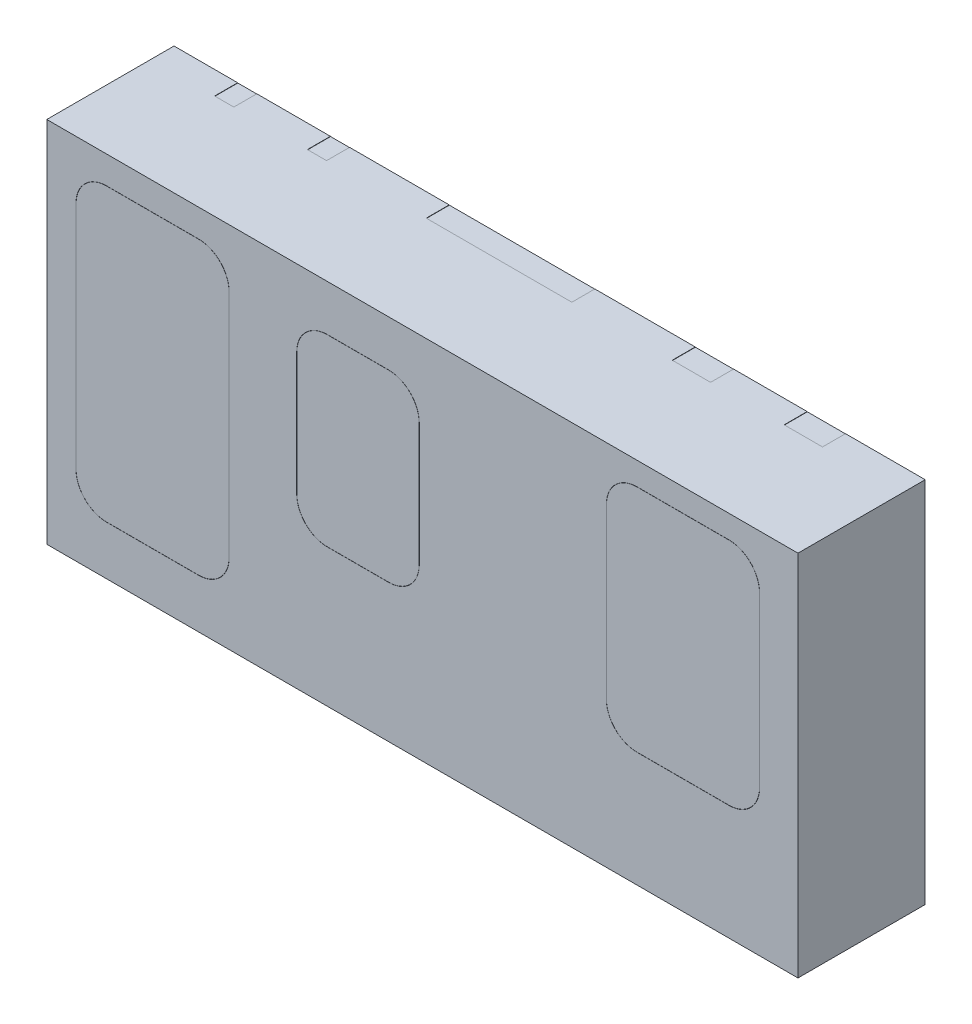
SolidWorks part; units mm, degrees
ref_plane "Спереди" through (0, 0, 0) normal (0, 0, 1) x (1, 0, 0)
ref_plane "Сверху" through (0, 0, 0) normal (0, 1, 0) x (1, 0, 0)
ref_plane "Справа" through (0, 0, 0) normal (1, 0, 0) x (0, 0, -1)
sketch "Эскиз1" plane through (0, 0, 0) normal (0, 0, 1) x (1, 0, 0)
  line L1 (0, 0) -> (4.9, 0)
  line L2 (0, 0) -> (0, 2.4)
  line L3 (0, 2.4) -> (4.9, 2.4)
  line L4 (4.9, 0) -> (4.9, 2.4)
  dimension "D1" = 4.9
  dimension "D2" = 2.4
extrude "Основание-Вытянуть" add sketch "Эскиз1" along normal blind 0.83
sketch "Эскиз2" plane through (0, 0, 0.83) normal (0, 0, 1) x (1, 0, 0)
  line L0 (0.69, 2.22) -> (0.69, 0.32) construction
  line L1 (3.85, 2.25) -> (4.45, 2.25)
  line L2 (3.65, 2.05) -> (3.65, 0.95)
  line L3 (3.85, 0.75) -> (4.45, 0.75)
  line L4 (4.65, 2.05) -> (4.65, 0.95)
  line L5 (1.83, 2.1) -> (2.23, 2.1)
  line L6 (1.63, 1.9) -> (1.63, 1.1)
  line L7 (1.83, 0.9) -> (2.23, 0.9)
  line L8 (2.43, 1.9) -> (2.43, 1.1)
  line L9 (0.39, 2.22) -> (0.99, 2.22)
  line L10 (0.19, 2.02) -> (0.19, 0.52)
  line L11 (0.39, 0.32) -> (0.99, 0.32)
  line L12 (1.19, 2.02) -> (1.19, 0.52)
  line L13 (2.03, 2.1) -> (2.03, 0.9) construction
  line L14 (4.15, 2.25) -> (4.15, 0.75) construction
  line L15 (0, 2.4) -> (0, 0) construction
  line L16 (0.19, 1.27) -> (1.19, 1.27) construction
  line L17 (1.63, 1.5) -> (2.43, 1.5) construction
  line L18 (3.65, 1.5) -> (4.65, 1.5) construction
  line L19 (0, 0) -> (4.9, 0) construction
  arc A0 (0.19, 0.52) -> (0.39, 0.32) centre (0.39, 0.52) ccw
  arc A1 (0.99, 0.32) -> (1.19, 0.52) centre (0.99, 0.52) ccw
  arc A2 (0.99, 2.22) -> (1.19, 2.02) centre (0.99, 2.02) cw
  arc A3 (0.39, 2.22) -> (0.19, 2.02) centre (0.39, 2.02) ccw
  arc A4 (1.83, 2.1) -> (1.63, 1.9) centre (1.83, 1.9) ccw
  arc A5 (2.23, 2.1) -> (2.43, 1.9) centre (2.23, 1.9) cw
  arc A6 (2.23, 0.9) -> (2.43, 1.1) centre (2.23, 1.1) ccw
  arc A7 (1.63, 1.1) -> (1.83, 0.9) centre (1.83, 1.1) ccw
  arc A8 (3.65, 0.95) -> (3.85, 0.75) centre (3.85, 0.95) ccw
  arc A9 (4.45, 0.75) -> (4.65, 0.95) centre (4.45, 0.95) ccw
  arc A10 (4.45, 2.25) -> (4.65, 2.05) centre (4.45, 2.05) cw
  arc A11 (3.85, 2.25) -> (3.65, 2.05) centre (3.85, 2.05) ccw
  dimension "D11" = 0.2
  dimension "D1" = 1
  dimension "D2" = 0.69
  dimension "D3" = 2.03
  dimension "D4" = 4.15
  dimension "D5" = 0.8
  dimension "D6" = 1.5
  dimension "D7" = 1.27
  dimension "D8" = 1.9
  dimension "D9" = 1.2
  dimension "D10" = 1.5
extrude "Вырез-Вытянуть1" cut sketch "Эскиз2" against normal blind 0.1
sketch "Эскиз3" plane through (0, 0, 0) normal (0, 0, -1) x (-1, 0, 0)
  line L0 (-4.9, 2.4) -> (0, 2.4) construction
  line L1 (-0.225, 1.2) -> (-1.335, 1.2)
  line L2 (-0.225, 1.2) -> (-0.225, 2.24)
  line L3 (-0.225, 2.24) -> (-0.415, 2.24)
  line L4 (-1.335, 1.2) -> (-1.335, 2.24)
  line L5 (-1.62, 0.9) -> (-2.92, 0.9)
  line L6 (-1.62, 0.9) -> (-1.62, 2.24)
  line L7 (-1.62, 2.24) -> (-1.795, 2.24)
  line L8 (-2.92, 0.9) -> (-2.92, 2.24)
  line L9 (-3.24, 0.9) -> (-4.54, 0.9)
  line L10 (-3.24, 0.9) -> (-3.24, 2.24)
  line L11 (-3.24, 2.24) -> (-3.4, 2.24)
  line L12 (-4.54, 0.9) -> (-4.54, 2.24)
  line L13 (-0.65, 0) -> (-0.65, 0.8037) construction
  line L14 (-1.795, 2.24) -> (-1.795, 2.4)
  line L15 (-1.795, 2.4) -> (-2.745, 2.4)
  line L16 (-2.745, 2.24) -> (-2.745, 2.4)
  line L17 (0, 0) -> (-4.9, 0) construction
  line L18 (-1.335, 0) -> (-1.335, 0.6958) construction
  line L19 (-0.415, 2.24) -> (-0.415, 2.4)
  line L20 (-0.415, 2.4) -> (-0.54, 2.4)
  line L21 (-1.145, 2.24) -> (-1.145, 2.4)
  line L22 (-2.02, 0) -> (-2.02, 0.6958) construction
  line L23 (-3.4, 2.24) -> (-3.4, 2.4)
  line L24 (-3.4, 2.4) -> (-3.65, 2.4)
  line L25 (-4.38, 2.24) -> (-4.38, 2.4)
  line L26 (-0.5, 0) -> (-0.8, 0)
  line L27 (-0.5, 0) -> (-0.5, 0.55)
  line L28 (-0.8, 0.55) -> (-0.9, 0.55)
  line L29 (-0.8, 0) -> (-0.8, 0.55)
  line L30 (-4.38, 2.24) -> (-4.54, 2.24)
  line L31 (-1.485, 0) -> (-1.185, 0)
  line L32 (-1.485, 0) -> (-1.485, 0.55)
  line L33 (-1.485, 0.55) -> (-1.385, 0.55)
  line L34 (-1.185, 0) -> (-1.185, 1)
  line L35 (-2.17, 0) -> (-1.87, 0)
  line L36 (-2.17, 0) -> (-2.17, 0.55)
  line L37 (-2.17, 0.55) -> (-1.87, 0.55)
  line L38 (-1.87, 0) -> (-1.87, 0.55)
  line L39 (-2.855, 0) -> (-2.555, 0)
  line L40 (-2.855, 0) -> (-2.855, 0.55)
  line L41 (-2.855, 0.55) -> (-2.555, 0.55)
  line L42 (-2.555, 0) -> (-2.555, 0.55)
  line L43 (-3.54, 0) -> (-3.24, 0)
  line L44 (-3.54, 0) -> (-3.54, 0.55)
  line L45 (-3.54, 0.55) -> (-3.24, 0.55)
  line L46 (-3.24, 0) -> (-3.24, 0.55)
  line L47 (-2.745, 2.24) -> (-2.92, 2.24)
  line L48 (-1.145, 2.24) -> (-1.335, 2.24)
  line L49 (-2.705, 0) -> (-2.705, 0.5973) construction
  line L50 (-3.39, 0) -> (-3.39, 0.5973) construction
  line L51 (0, 2.4) -> (0, 0) construction
  line L52 (-1.385, 0.55) -> (-1.385, 1)
  line L53 (-4.13, 2.4) -> (-4.38, 2.4)
  line L54 (-0.25, 0.55) -> (-0.5, 0.55)
  line L55 (-1.385, 1) -> (-1.185, 1)
  line L56 (-0.25, 0.55) -> (-0.25, 1)
  line L57 (-0.25, 1) -> (-0.9, 1)
  line L58 (-0.9, 0.55) -> (-0.9, 1)
  line L59 (-1.02, 2.4) -> (-1.145, 2.4)
  line L60 (-0.78, 2.4) -> (-0.78, 1.2) construction
  line L61 (-3.89, 2.4) -> (-3.89, 0.9) construction
  line L62 (-2.27, 2.4) -> (-2.27, 0.9) construction
  arc A0 (-4.13, 2.4) -> (-3.65, 2.4) centre (-3.89, 2.4) ccw
  arc A1 (-1.02, 2.4) -> (-0.54, 2.4) centre (-0.78, 2.4) ccw
  dimension "D14" = 0.48
  dimension "D1" = 0.65
  dimension "D2" = 0.685
  dimension "D3" = 0.685
  dimension "D4" = 0.685
  dimension "D5" = 0.685
  dimension "D6" = 0.3
  dimension "D7" = 0.55
  dimension "D8" = 0.2
  dimension "D9" = 1
  dimension "D10" = 0.65
  dimension "D11" = 0.73
  dimension "D12" = 0.95
  dimension "D13" = 0.98
  dimension "D15" = 1.5
  dimension "D16" = 0.78
  dimension "D17" = 1.49
  dimension "D18" = 1.62
  dimension "D19" = 1.2
  dimension "D20" = 1.3
  dimension "D21" = 0.16
extrude "Вырез-Вытянуть2" cut sketch "Эскиз3" against normal blind 0.15
sketch "Эскиз4" plane through (0, 0, 0.15) normal (0, 0, -1) x (-1, 0, 0)
  line L16 (-0.501, 0.001) -> (-0.501, 0.551)
  line L17 (-0.501, 0.551) -> (-0.251, 0.551)
  line L18 (-0.251, 0.551) -> (-0.251, 0.999)
  line L19 (-0.251, 0.999) -> (-0.899, 0.999)
  line L20 (-0.899, 0.999) -> (-0.899, 0.551)
  line L21 (-0.899, 0.551) -> (-0.799, 0.551)
  line L22 (-0.799, 0.551) -> (-0.799, 0.001)
  line L23 (-0.799, 0.001) -> (-0.501, 0.001)
  line L24 (-0.501, 0.001) -> (-0.501, 0.551)
  line L25 (-0.501, 0.551) -> (-0.251, 0.551)
  line L26 (-0.251, 0.551) -> (-0.251, 0.999)
  line L27 (-0.251, 0.999) -> (-0.899, 0.999)
  line L28 (-0.899, 0.999) -> (-0.899, 0.551)
  line L29 (-0.899, 0.551) -> (-0.799, 0.551)
  line L30 (-0.799, 0.551) -> (-0.799, 0.001)
  line L31 (-0.799, 0.001) -> (-0.501, 0.001)
  dimension "D1" = 0.001
extrude "Бобышка-Вытянуть1" add sketch "Эскиз4" along normal up to surface (0.15 mm away)
sketch "Эскиз5" plane through (0, 0, 0.15) normal (0, 0, -1) x (-1, 0, 0)
  line L18 (-1.484, 0.549) -> (-1.484, 0.001)
  line L19 (-1.484, 0.001) -> (-1.186, 0.001)
  line L20 (-1.186, 0.001) -> (-1.186, 0.999)
  line L21 (-1.186, 0.999) -> (-1.384, 0.999)
  line L22 (-1.384, 0.999) -> (-1.384, 0.549)
  line L23 (-1.384, 0.549) -> (-1.484, 0.549)
  line L24 (-1.484, 0.549) -> (-1.484, 0.001)
  line L25 (-1.484, 0.001) -> (-1.186, 0.001)
  line L26 (-1.186, 0.001) -> (-1.186, 0.999)
  line L27 (-1.186, 0.999) -> (-1.384, 0.999)
  line L28 (-1.384, 0.999) -> (-1.384, 0.549)
  line L29 (-1.384, 0.549) -> (-1.484, 0.549)
  line L32 (-2.169, 0.549) -> (-2.169, 0.001)
  line L33 (-2.169, 0.001) -> (-1.871, 0.001)
  line L34 (-1.871, 0.001) -> (-1.871, 0.549)
  line L35 (-1.871, 0.549) -> (-2.169, 0.549)
  line L36 (-2.169, 0.549) -> (-2.169, 0.001)
  line L37 (-2.169, 0.001) -> (-1.871, 0.001)
  line L38 (-1.871, 0.001) -> (-1.871, 0.549)
  line L39 (-1.871, 0.549) -> (-2.169, 0.549)
  line L44 (-2.854, 0.549) -> (-2.854, 0.001)
  line L45 (-2.854, 0.001) -> (-2.556, 0.001)
  line L46 (-2.556, 0.001) -> (-2.556, 0.549)
  line L47 (-2.556, 0.549) -> (-2.854, 0.549)
  line L48 (-2.854, 0.549) -> (-2.854, 0.001)
  line L49 (-2.854, 0.001) -> (-2.556, 0.001)
  line L50 (-2.556, 0.001) -> (-2.556, 0.549)
  line L51 (-2.556, 0.549) -> (-2.854, 0.549)
  line L56 (-3.539, 0.549) -> (-3.539, 0.001)
  line L57 (-3.539, 0.001) -> (-3.241, 0.001)
  line L58 (-3.241, 0.001) -> (-3.241, 0.549)
  line L59 (-3.241, 0.549) -> (-3.539, 0.549)
  line L60 (-3.539, 0.549) -> (-3.539, 0.001)
  line L61 (-3.539, 0.001) -> (-3.241, 0.001)
  line L62 (-3.241, 0.001) -> (-3.241, 0.549)
  line L63 (-3.241, 0.549) -> (-3.539, 0.549)
  line L78 (-3.241, 0.901) -> (-3.241, 2.239)
  line L79 (-3.241, 2.239) -> (-3.401, 2.239)
  line L80 (-3.401, 2.239) -> (-3.401, 2.399)
  line L81 (-3.401, 2.399) -> (-3.649, 2.399)
  line L82 (-4.131, 2.399) -> (-4.379, 2.399)
  line L83 (-4.379, 2.399) -> (-4.379, 2.239)
  line L84 (-4.379, 2.239) -> (-4.539, 2.239)
  line L85 (-4.539, 2.239) -> (-4.539, 0.901)
  line L86 (-4.539, 0.901) -> (-3.241, 0.901)
  line L87 (-3.241, 0.901) -> (-3.241, 2.239)
  line L88 (-3.241, 2.239) -> (-3.401, 2.239)
  line L89 (-3.401, 2.239) -> (-3.401, 2.399)
  line L90 (-3.401, 2.399) -> (-3.649, 2.399)
  line L91 (-4.131, 2.399) -> (-4.379, 2.399)
  line L92 (-4.379, 2.399) -> (-4.379, 2.239)
  line L93 (-4.379, 2.239) -> (-4.539, 2.239)
  line L94 (-4.539, 2.239) -> (-4.539, 0.901)
  line L95 (-4.539, 0.901) -> (-3.241, 0.901)
  line L103 (-1.621, 0.901) -> (-1.621, 2.239)
  line L104 (-1.621, 2.239) -> (-1.796, 2.239)
  line L105 (-1.796, 2.239) -> (-1.796, 2.399)
  line L106 (-1.796, 2.399) -> (-2.744, 2.399)
  line L107 (-2.744, 2.399) -> (-2.744, 2.239)
  line L108 (-2.744, 2.239) -> (-2.919, 2.239)
  line L109 (-2.919, 2.239) -> (-2.919, 0.901)
  line L110 (-2.919, 0.901) -> (-1.621, 0.901)
  line L111 (-1.621, 0.901) -> (-1.621, 2.239)
  line L112 (-1.621, 2.239) -> (-1.796, 2.239)
  line L113 (-1.796, 2.239) -> (-1.796, 2.399)
  line L114 (-1.796, 2.399) -> (-2.744, 2.399)
  line L115 (-2.744, 2.399) -> (-2.744, 2.239)
  line L116 (-2.744, 2.239) -> (-2.919, 2.239)
  line L117 (-2.919, 2.239) -> (-2.919, 0.901)
  line L118 (-2.919, 0.901) -> (-1.621, 0.901)
  line L129 (-0.226, 1.201) -> (-0.226, 2.239)
  line L130 (-0.226, 2.239) -> (-0.416, 2.239)
  line L131 (-0.416, 2.239) -> (-0.416, 2.399)
  line L132 (-0.416, 2.399) -> (-0.539, 2.399)
  line L133 (-1.021, 2.399) -> (-1.144, 2.399)
  line L134 (-1.144, 2.399) -> (-1.144, 2.239)
  line L135 (-1.144, 2.239) -> (-1.334, 2.239)
  line L136 (-1.334, 2.239) -> (-1.334, 1.201)
  line L137 (-1.334, 1.201) -> (-0.226, 1.201)
  line L138 (-0.226, 1.201) -> (-0.226, 2.239)
  line L139 (-0.226, 2.239) -> (-0.416, 2.239)
  line L140 (-0.416, 2.239) -> (-0.416, 2.399)
  line L141 (-0.416, 2.399) -> (-0.539, 2.399)
  line L142 (-1.021, 2.399) -> (-1.144, 2.399)
  line L143 (-1.144, 2.399) -> (-1.144, 2.239)
  line L144 (-1.144, 2.239) -> (-1.334, 2.239)
  line L145 (-1.334, 2.239) -> (-1.334, 1.201)
  line L146 (-1.334, 1.201) -> (-0.226, 1.201)
  arc A2 (-4.131, 2.399) -> (-3.649, 2.399) centre (-3.89, 2.4) ccw
  arc A3 (-4.131, 2.399) -> (-3.649, 2.399) centre (-3.89, 2.4) ccw
  arc A5 (-1.021, 2.399) -> (-0.539, 2.399) centre (-0.78, 2.4) ccw
  arc A6 (-1.021, 2.399) -> (-0.539, 2.399) centre (-0.78, 2.4) ccw
  dimension "D1" = 0.001
  dimension "D2" = 0.001
  dimension "D3" = 0.001
  dimension "D4" = 0.001
  dimension "D5" = 0.001
  dimension "D6" = 0.001
  dimension "D7" = 0.001
extrude "Бобышка-Вытянуть2" add sketch "Эскиз5" along normal up to surface (0.15 mm away)
sketch "Эскиз6" plane through (0, 0, 0.73) normal (0, 0, 1) x (1, 0, 0)
  line L8 (3.85, 0.751) -> (4.45, 0.751)
  line L9 (4.649, 0.95) -> (4.649, 2.05)
  line L10 (4.45, 2.249) -> (3.85, 2.249)
  line L11 (3.651, 2.05) -> (3.651, 0.95)
  line L12 (3.85, 0.751) -> (4.45, 0.751)
  line L13 (4.649, 0.95) -> (4.649, 2.05)
  line L14 (4.45, 2.249) -> (3.85, 2.249)
  line L15 (3.651, 2.05) -> (3.651, 0.95)
  line L20 (1.631, 1.9) -> (1.631, 1.1)
  line L21 (1.83, 0.901) -> (2.23, 0.901)
  line L22 (2.429, 1.1) -> (2.429, 1.9)
  line L23 (2.23, 2.099) -> (1.83, 2.099)
  line L24 (1.631, 1.9) -> (1.631, 1.1)
  line L25 (1.83, 0.901) -> (2.23, 0.901)
  line L26 (2.429, 1.1) -> (2.429, 1.9)
  line L27 (2.23, 2.099) -> (1.83, 2.099)
  line L32 (0.39, 0.321) -> (0.99, 0.321)
  line L33 (1.189, 0.52) -> (1.189, 2.02)
  line L34 (0.99, 2.219) -> (0.39, 2.219)
  line L35 (0.191, 2.02) -> (0.191, 0.52)
  line L36 (0.39, 0.321) -> (0.99, 0.321)
  line L37 (1.189, 0.52) -> (1.189, 2.02)
  line L38 (0.99, 2.219) -> (0.39, 2.219)
  line L39 (0.191, 2.02) -> (0.191, 0.52)
  arc A8 (3.651, 0.95) -> (3.85, 0.751) centre (3.85, 0.95) ccw
  arc A9 (4.45, 0.751) -> (4.649, 0.95) centre (4.45, 0.95) ccw
  arc A10 (4.649, 2.05) -> (4.45, 2.249) centre (4.45, 2.05) ccw
  arc A11 (3.85, 2.249) -> (3.651, 2.05) centre (3.85, 2.05) ccw
  arc A12 (3.651, 0.95) -> (3.85, 0.751) centre (3.85, 0.95) ccw
  arc A13 (4.45, 0.751) -> (4.649, 0.95) centre (4.45, 0.95) ccw
  arc A14 (4.649, 2.05) -> (4.45, 2.249) centre (4.45, 2.05) ccw
  arc A15 (3.85, 2.249) -> (3.651, 2.05) centre (3.85, 2.05) ccw
  arc A20 (1.83, 2.099) -> (1.631, 1.9) centre (1.83, 1.9) ccw
  arc A21 (1.631, 1.1) -> (1.83, 0.901) centre (1.83, 1.1) ccw
  arc A22 (2.23, 0.901) -> (2.429, 1.1) centre (2.23, 1.1) ccw
  arc A23 (2.429, 1.9) -> (2.23, 2.099) centre (2.23, 1.9) ccw
  arc A24 (1.83, 2.099) -> (1.631, 1.9) centre (1.83, 1.9) ccw
  arc A25 (1.631, 1.1) -> (1.83, 0.901) centre (1.83, 1.1) ccw
  arc A26 (2.23, 0.901) -> (2.429, 1.1) centre (2.23, 1.1) ccw
  arc A27 (2.429, 1.9) -> (2.23, 2.099) centre (2.23, 1.9) ccw
  arc A32 (0.191, 0.52) -> (0.39, 0.321) centre (0.39, 0.52) ccw
  arc A33 (0.99, 0.321) -> (1.189, 0.52) centre (0.99, 0.52) ccw
  arc A34 (1.189, 2.02) -> (0.99, 2.219) centre (0.99, 2.02) ccw
  arc A35 (0.39, 2.219) -> (0.191, 2.02) centre (0.39, 2.02) ccw
  arc A36 (0.191, 0.52) -> (0.39, 0.321) centre (0.39, 0.52) ccw
  arc A37 (0.99, 0.321) -> (1.189, 0.52) centre (0.99, 0.52) ccw
  arc A38 (1.189, 2.02) -> (0.99, 2.219) centre (0.99, 2.02) ccw
  arc A39 (0.39, 2.219) -> (0.191, 2.02) centre (0.39, 2.02) ccw
  dimension "D1" = 0.001
  dimension "D2" = 0.001
  dimension "D3" = 0.001
extrude "Бобышка-Вытянуть3" add sketch "Эскиз6" along normal up to surface (0.1 mm away)
